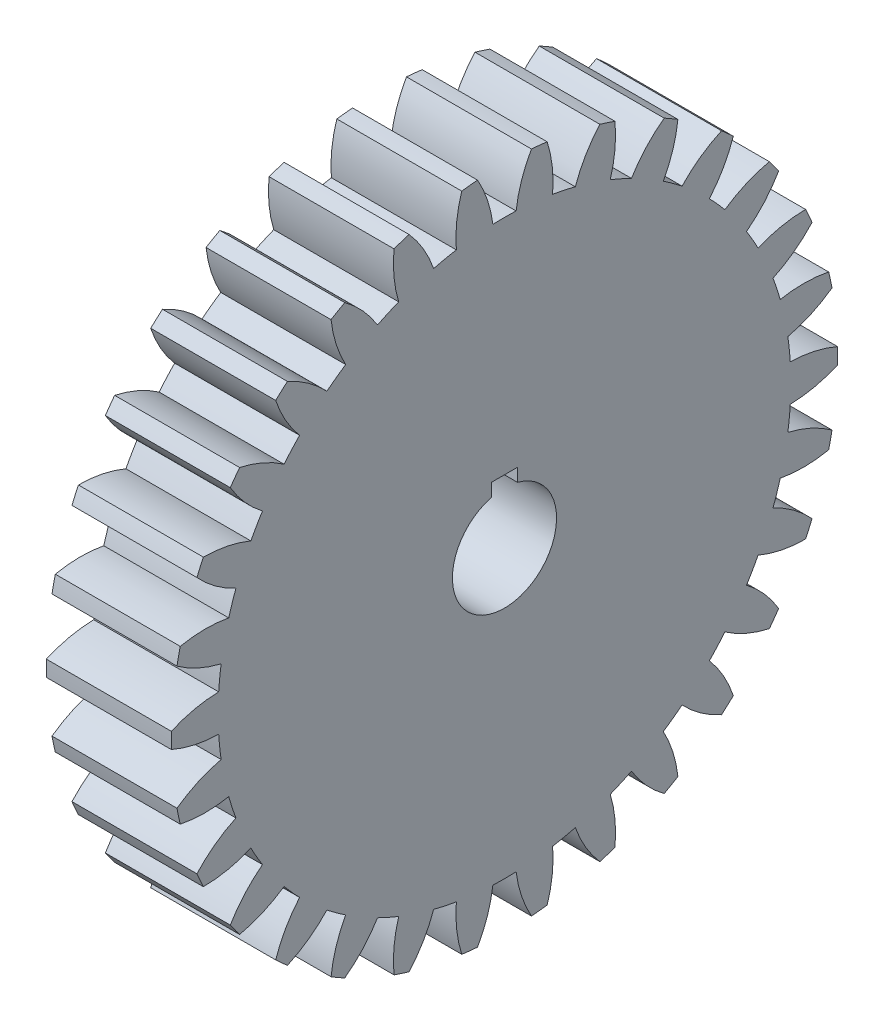
SolidWorks part; units mm, degrees
ref_plane "Plane1" through (0, 0, 0) normal (0, 0, 1) x (1, 0, 0)
ref_plane "Plane2" through (0, 0, 0) normal (0, 1, 0) x (1, 0, 0)
ref_plane "Plane3" through (0, 0, 0) normal (1, 0, 0) x (0, 0, -1)
other "Configuration Table"
sketch "HoldingSke" plane through (0, 0, 0) normal (0, 1, 0) x (1, 0, 0)
  line L0 (0, 0) -> (10.9985, -6.35)
  line L1 (-15, 0) -> (100, 0) construction
  line L2 (0, 0) -> (-2.1039, 2.3779)
  line L3 (0, 0) -> (-11.863, 4.5341)
  line L4 (0, 0) -> (7.479, 4.318)
  line L5 (0, 0) -> (-47.5972, -17.7524)
  line L6 (0, 0) -> (-252.6679, -170.4757)
  line L7 (-2.1039, 2.3779) -> (63.5041, 300.0332)
  line L8 (-76.2, 54.61) -> (205.6384, 54.61)
  line L9 (-67.7845, 28.3722) -> (-49.3413, 33.142)
  line L10 (-76.2, 71.12) -> (104.1128, 71.12)
  line L11 (0, 0) -> (-304.8, 0)
  line L12 (-76.2, 101.6) -> (-74.295, 101.6)
  line L13 (24.9733, 27.94) -> (52.9518, 28.4284)
  line L14 (24.9733, 27.94) -> (24.9746, 27.94)
  line L15 (24.9733, 27.94) -> (100.4006, 29.5858)
  circle A0 centre (0, 0) radius 127
  circle A1 centre (0, 0) radius 38.1
  circle A2 centre (0, 0) radius 38.1
  circle A3 centre (0, 0) radius 127
  dimension "MHD" = 76.2
  dimension "Hub_dia" = 76.2
  dimension "Bore" = 254
  dimension "MBD" = 254
  dimension "Num_teeth" = 30
  dimension "Pitch" = 12.7
  dimension "Overall_len" = 50.8
  dimension "Show_teeth" = 30
  dimension "Thickness" = 304.8
  dimension "OAL" = 304.8001
  dimension "T_dim" = 281.8384
  dimension "Ap" = 14.5
  dimension "H" = 19.05
  dimension "Pitch_radius" = 180.3128
  dimension "Width" = 304.8
  dimension "Backlash" = 1.905
  dimension "Addendum_fac" = 1
  dimension "Dedendum_fac" = 1.25
  dimension "Clearance_fac" = 0.25
  dimension "Dedendum_add" = 0.0013
sketch "BasProSke" plane through (0, 0, 0) normal (0, 1, 0) x (1, 0, 0)
  line L0 (-10, 0) -> (60, 0) construction
  line L1 (0, 0) -> (0, 812.8)
  line L2 (0, 0) -> (304.8, 0)
  line L3 (304.8, 0) -> (304.8, 812.8)
  line L4 (304.8, 812.8) -> (0, 812.8)
  dimension "Thickness" = 304.8
  dimension "Diameter" = 1625.6
revolve "Base-Revolve" add sketch "BasProSke" angle 360 about L0
sketch "TooCutSke" plane through (0, 0, 0) normal (1, 0, 0) x (0, 0, -1)
  line L1 (0, 0) -> (0, 107) construction
  line L2 (0, 0) -> (-43.213, 760.7737) construction
  line L3 (0, 0) -> (-159.1181, 1513.9072) construction
  line L4 (-43.213, 760.7737) -> (-79.559, 756.9536) construction
  arc A0 (28.3197, 697.9244) -> (-28.3197, 697.9244) centre (0, 0) ccw
  arc A1 (65.744, 810.1622) -> (-65.744, 810.1622) centre (0, 0) ccw
  circle A2 centre (0, 0) radius 762 construction
  circle A3 centre (0, 0) radius 737.7285 construction
  arc A4 (-28.3197, 697.9244) -> (-65.744, 810.1622) centre (-330.6834, 659.4633) ccw
  arc A5 (65.744, 810.1622) -> (28.3197, 697.9244) centre (330.6834, 659.4633) ccw
  dimension "Root_dia" = 1396.9975
  dimension "Overcut_dia" = 1625.6508
  dimension "Pitch_dia" = 1524
  dimension "Base_dia" = 1475.457
  dimension "Flank_rad" = 304.8
  dimension "Half_ang" = 6
  dimension "Half_CT" = 36.5462
extrude "ToothCut" cut sketch "TooCutSke" along normal through all
fillet "Breaks" [suppressed] radius 1.016
fillet "RootFillets" [suppressed] radius 12.7013
pattern_circular "TeethCuts" count 30 every 12 about axis through (-10, 0, 0) along (1, 0, 0) of "ToothCut", "RootFillets", "Breaks"
sketch "HubNeaOneSke" plane through (0, 0, 0) normal (-1, 0, 0) x (0, 0, 1)
  circle A0 centre (0, 0) radius 38.1
  dimension "Diameter" = 76.2
extrude "HubNearOne" [suppressed] add sketch "HubNeaOneSke" along normal blind 25.4001
sketch "HubNeaBotSke" plane through (0, 0, 0) normal (-1, 0, 0) x (0, 0, 1)
  circle A0 centre (0, 0) radius 38.1
  dimension "Diameter" = 76.2
extrude "HubNearBoth" [suppressed] add sketch "HubNeaBotSke" along normal blind 12.7
ref_plane "FarPln" through (304.8, 0, 0) normal (1, 0, 0) x (0, 0, -1)
sketch "HubFarSke" plane through (304.8, 0, 0) normal (1, 0, 0) x (0, 0, -1)
  circle A0 centre (0, 0) radius 38.1
  dimension "Diameter" = 76.2
extrude "HubFar" [suppressed] add sketch "HubFarSke" along normal blind 12.7
sketch "BorSke" plane through (0, 0, 0) normal (1, 0, 0) x (0, 0, -1)
  circle A0 centre (0, 0) radius 127
  dimension "Diameter" = 254
extrude "Bore" cut sketch "BorSke" along normal mid plane 609.6001
sketch "KeySke" plane through (0, 0, 0) normal (1, 0, 0) x (0, 0, -1)
  line L0 (-31.75, 0) -> (-31.75, 154.8384)
  line L1 (-31.75, 154.8384) -> (31.75, 154.8384)
  line L2 (31.75, 154.8384) -> (31.75, 0)
  line L3 (0, 0) -> (0, 34) construction
  line L4 (-31.75, 0) -> (31.75, 0)
  dimension "Offset" = 154.8384
  dimension "Width" = 63.5
extrude "Keyway" cut sketch "KeySke" along normal mid plane 609.6001
pattern_circular "Keyway2" [suppressed] count 2 every 90 about axis through (-10, 0, 0) along (1, 0, 0)
equation "' \"Pitch@HoldingSke\" = 4"
equation "' \"Num_teeth@HoldingSke\" = 12"
equation "' \"Ap@HoldingSke\" =  20"
equation "' \"Ap@HoldingSke\" = 20"
equation "' \"Width@HoldingSke\" = 0.5"
equation "' \"Hub_dia@HoldingSke\"= 1"
equation "' \"Hub_dia@HoldingSke\" = 1"
equation "' \"Overall_len@HoldingSke\" = 1.0"
equation "' \"Bore@HoldingSke\" = 0.75"
equation "' \"T_dim@HoldingSke\" = 0.85"
equation "' \"Width@KeySke\" = 0.25"
equation "' \"Show_teeth@HoldingSke\" = 13"
equation "' \"Backlash@HoldingSke\" = 0.009"
equation "' \"Addendum_fac@HoldingSke\" = 1.0"
equation "' \"Dedendum_fac@HoldingSke\" = 1.25"
equation "' \"Dedendum_add@HoldingSke\" = 0.00005"
equation "' \"Clearance_fac@HoldingSke\" = 0.25"
equation "' \"Pitch@HoldingSke\" = 0.5"
equation "' \"Num_teeth@HoldingSke\" = 23"
equation "' \"Show_teeth@HoldingSke\" = 23"
equation "' \"Backlash@HoldingSke\" = 0.0375"
equation "\"Overcut_dia@TooCutSke\" = (\"Num_teeth@HoldingSke\" + 2 * \"Addendum_fac@HoldingSke\") / \"Pitch@HoldingSke\" + 0.002"
equation "\"Pitch_dia@TooCutSke\" = \"Num_teeth@HoldingSke\" / \"Pitch@HoldingSke\""
equation "\"Base_dia@TooCutSke\" = \"Num_teeth@HoldingSke\" / \"Pitch@HoldingSke\" * cos((\"Ap@HoldingSke\"  * 3.14159265 / 180))"
equation "\"Root_dia@TooCutSke\" = (\"Num_teeth@HoldingSke\" + 2) / \"Pitch@HoldingSke\" - 2 * (\"Addendum_fac@HoldingSke\" + \"Dedendum_fac@HoldingSke\") / \"Pitch@HoldingSke\" - \"Dedendum_add@HoldingSke\" * 2"
equation "\"Half_ang@TooCutSke\" = 180 / \"Num_teeth@HoldingSke\""
equation "\"Half_CT@TooCutSke\" = \"Num_teeth@HoldingSke\" / \"Pitch@HoldingSke\" * sin((3.14159265 / 2 / \"Num_teeth@HoldingSke\")) / 2 - 7 * \"Backlash@HoldingSke\" / 4"
equation "\"Flank_rad@TooCutSke\" = \"Num_teeth@HoldingSke\" / \"Pitch@HoldingSke\" / 5"
equation "\"Radius@RootFillets\" = \"Clearance_fac@HoldingSke\" / \"Pitch@HoldingSke\" + \"Dedendum_add@HoldingSke\""
equation "\"Break_rad@Breaks\" = 0.02 / \"Pitch@HoldingSke\""
equation "\"Thickness@HoldingSke\" = \"Width@HoldingSke\""
equation "\"OAL@HoldingSke\" = \"Thickness@HoldingSke\""
equation "\"MHD@HoldingSke\" = (\"Num_teeth@HoldingSke\" + 2) / \"Pitch@HoldingSke\" - 2 * (\"Addendum_fac@HoldingSke\" + \"Dedendum_fac@HoldingSke\")  / \"Pitch@HoldingSke\" - \"Dedendum_add@HoldingSke\" * 2"
equation "\"MBD@HoldingSke\" = (\"Num_teeth@HoldingSke\" + 2) / \"Pitch@HoldingSke\" - 2 * (\"Addendum_fac@HoldingSke\" + \"Dedendum_fac@HoldingSke\")  / \"Pitch@HoldingSke\" - \"Dedendum_add@HoldingSke\" * 2 - 0.002"
equation "\"MHD@HoldingSke\" = ((sgn( \"MHD@HoldingSke\" - \"Hub_dia@HoldingSke\" )-1)*( \"MHD@HoldingSke\" - \"Hub_dia@HoldingSke\" ))/-2+ \"Hub_dia@HoldingSke\""
equation "\"MBD@HoldingSke\" = ((sgn( \"MBD@HoldingSke\" - \"Bore@HoldingSke\" )-1)*( \"MBD@HoldingSke\" - \"Bore@HoldingSke\" ))/-2+ \"Bore@HoldingSke\""
equation "\"OAL@HoldingSke\" = ((sgn( \"OAL@HoldingSke\" - \"Overall_len@HoldingSke\" )+1)*( \"OAL@HoldingSke\" - \"Overall_len@HoldingSke\" ))/2 + \"Overall_len@HoldingSke\" + 0.000002"
equation "\"Num_teeth@TeethCuts\" = int( \"Show_teeth@HoldingSke\" ) + 1"
equation "\"Num_teeth@TeethCuts\" = ((sgn( \"Num_teeth@TeethCuts\" - \"Num_teeth@HoldingSke\" )-1)*( \"Num_teeth@TeethCuts\" - \"Num_teeth@HoldingSke\" ))/-2+ \"Num_teeth@HoldingSke\""
equation "\"Num_teeth@TeethCuts\" = ((sgn( \"Num_teeth@TeethCuts\" - 2.0)+1)*( \"Num_teeth@TeethCuts\" - 2.0))/2 +2.0"
equation "\"Angle@TeethCuts\" = 360.0 / \"Num_teeth@HoldingSke\""
equation "\"Diameter@BasProSke\" = (\"Num_teeth@HoldingSke\" + 2 * \"Addendum_fac@HoldingSke\") / \"Pitch@HoldingSke\""
equation "\"Thickness@BasProSke\"  = \"Thickness@HoldingSke\""
equation "' \"Fillet_rad@BasProSke\" =  \"Thickness@HoldingSke\" * 0.05"
equation "' \"Fillet_rad@BasProSke\" = \"Thickness@HoldingSke\" * 0.05"
equation "\"MHD@HoldingSke\" = ((sgn( \"MHD@HoldingSke\" - \"Root_dia@TooCutSke\" )-1)*( \"MHD@HoldingSke\" - \"Root_dia@TooCutSke\" ))/-2+ \"Root_dia@TooCutSke\""
equation "\"Diameter@HubNeaOneSke\" = \"MHD@HoldingSke\""
equation "\"Length@HubNearOne\" = \"OAL@HoldingSke\" - \"Thickness@BasProSke\""
equation "\"Diameter@HubNeaBotSke\" = \"MHD@HoldingSke\""
equation "\"Length@HubNearBoth\" = ( \"OAL@HoldingSke\" - \"Thickness@BasProSke\" ) / 2.0"
equation "\"Thickness@FarPln\" = \"Thickness@BasProSke\""
equation "\"Diameter@HubFarSke\" = \"MHD@HoldingSke\""
equation "\"Length@HubFar\" = ( \"OAL@HoldingSke\" - \"Thickness@BasProSke\" ) / 2.0"
equation "\"Diameter@BorSke\" = \"MBD@HoldingSke\""
equation "\"D1@Bore\" = \"OAL@HoldingSke\" * 2.0"
equation "\"D1@Keyway\" = \"OAL@HoldingSke\" * 2.0"
equation "\"Offset@KeySke\" = \"T_dim@HoldingSke\" - \"MBD@HoldingSke\" / 2.0"
